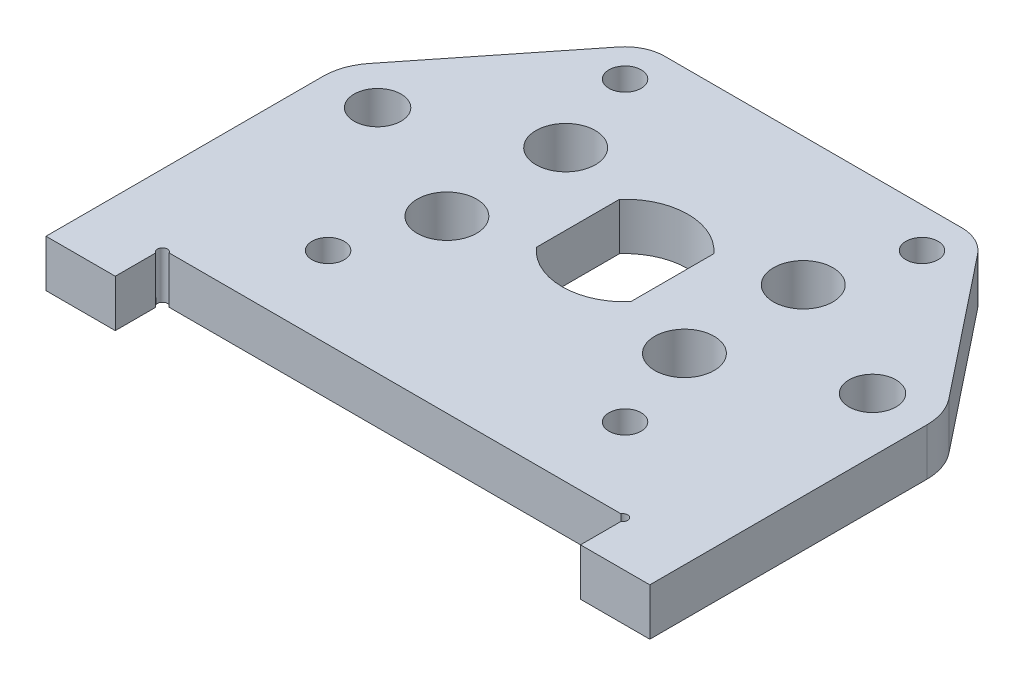
SolidWorks part; units mm, degrees
ref_plane "Front Plane" through (0, 0, 0) normal (0, 0, 1) x (1, 0, 0)
ref_plane "Top Plane" through (0, 0, 0) normal (0, 1, 0) x (1, 0, 0)
ref_plane "Right Plane" through (0, 0, 0) normal (1, 0, 0) x (0, 0, -1)
sketch "Sketch1" plane through (0, 0, 0) normal (0, 1, 0) x (1, 0, 0)
  line L0 (-4.7625, -4.2001) -> (-4.7625, 4.2001)
  line L1 (0, -6.35) -> (0, -23.2375)
  line L2 (-12, -6) -> (-12, 6) construction
  line L3 (0, 19) -> (-15, 19)
  line L4 (-23.5, -28) -> (-30.5, -28)
  line L5 (0, 6.35) -> (0, 19)
  line L6 (-15, -15) -> (0, 0) construction
  line L7 (0, 0) -> (-15, 15) construction
  line L8 (-29.3066, 3.421) -> (-18.132, 17.488)
  line L9 (-30.5, 0) -> (-30.5, -28)
  line L10 (-12, 0) -> (0, 0) construction
  line L12 (0, -23.2375) -> (-23.5, -23.2375)
  line L13 (-23.5, -28) -> (-23.5, -23.2375)
  arc A0 (-4.7625, -4.2001) -> (0, -6.35) centre (0, 0) ccw
  arc A1 (0, 6.35) -> (-4.7625, 4.2001) centre (0, 0) ccw
  circle A2 centre (-15, 15) radius 1.625
  circle A3 centre (-15, -15) radius 1.625
  circle A4 centre (-25, 0) radius 2.375
  circle A5 centre (-12, -6) radius 3
  arc A6 (-30.5, 0) -> (-29.3066, 3.421) centre (-25, 0) cw
  arc A7 (-15, 19) -> (-18.132, 17.488) centre (-15, 15) ccw
  circle A8 centre (-12, 6) radius 3
  dimension "D3" = 4.75
  dimension "D4" = 3.25
  dimension "D7" = 6.35
  dimension "D9" = 5.5
  dimension "D13" = 6
  dimension "D1" = 25
  dimension "D2" = 15
  dimension "D5" = 45
  dimension "D6" = 4.7625
  dimension "D8" = 28
  dimension "D10" = 19
  dimension "D11" = 4.7625
  dimension "D12" = 7
  dimension "D14" = 12
  dimension "D15" = 12
extrude "Boss-Extrude1" add sketch "Sketch1" along normal blind 4.7625
mirror "Mirror1" about plane through (0, 4.7625, 6.35) normal (-1, 0, 0) of "Boss-Extrude1"
sketch "Sketch2" plane through (0, 4.7625, 0) normal (0, 1, 0) x (1, 0, 0)
  line L0 (-23.5, -23.2375) -> (23.5, -23.2375) construction
  line L1 (-23.5, -28) -> (-23.5, -23.2375) construction
  line L2 (23.5, -28) -> (23.5, -23.2375) construction
  circle A0 centre (-23.25, -23.4875) radius 0.5
  circle A1 centre (23.25, -23.4875) radius 0.5
  dimension "D4" = 1
  dimension "D1" = 0.25
  dimension "D2" = 0.25
  dimension "D3" = 0.25
extrude "Cut-Extrude1" cut sketch "Sketch2" against normal through all
